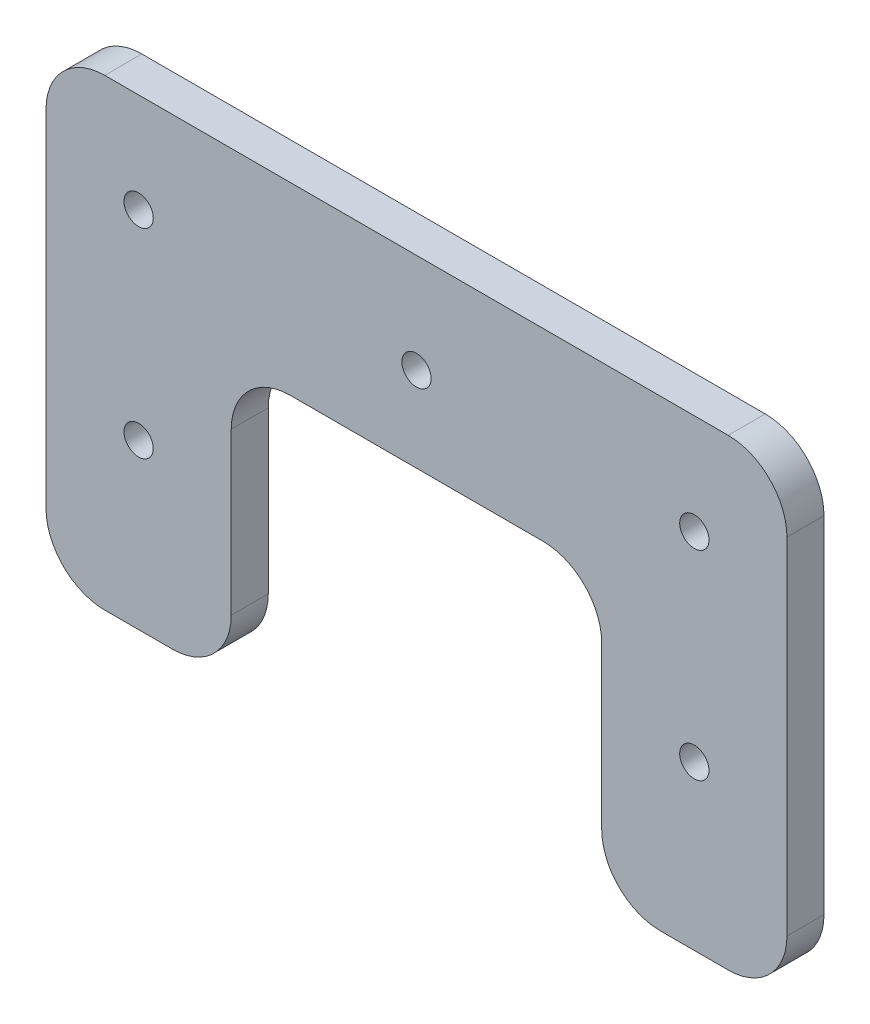
SolidWorks part; units mm, degrees
ref_plane "Alzado" through (0, 0, 0) normal (0, 0, 1) x (1, 0, 0)
ref_plane "Planta" through (0, 0, 0) normal (0, 1, 0) x (1, 0, 0)
ref_plane "Vista lateral" through (0, 0, 0) normal (1, 0, 0) x (0, 0, -1)
sketch "Croquis1" plane through (0, 0, 0) normal (0, 0, 1) x (1, 0, 0)
  line L1 (26.5381, 6.6994) -> (53.8381, 6.6994)
  line L2 (0.1881, 6.6044) -> (0.1881, 20.2544)
  line L3 (6.5381, 26.6044) -> (73.8381, 26.6044)
  line L4 (80.1881, 6.6044) -> (80.1881, 20.2544)
  line L6 (0.1881, 6.6044) -> (0.1881, -17.0456)
  line L7 (6.5381, -23.3956) -> (13.8381, -23.3956)
  line L8 (20.1881, 0.3494) -> (20.1881, -17.0456)
  line L10 (80.1881, 6.6044) -> (80.1881, -17.0456)
  line L11 (73.8381, -23.3956) -> (66.5381, -23.3956)
  line L12 (60.1881, 0.3494) -> (60.1881, -17.0456)
  circle A0 centre (40.1881, 15.8665) radius 1.58
  circle A1 centre (10.1881, 15.8665) radius 1.58
  circle A2 centre (70.1881, 15.7714) radius 1.58
  circle A3 centre (10.1881, -5.6765) radius 1.58
  circle A4 centre (70.1881, -5.7716) radius 1.58
  arc A5 (26.5381, 6.6994) -> (20.1881, 0.3494) centre (26.5381, 0.3494) ccw
  arc A6 (80.1881, 20.2544) -> (73.8381, 26.6044) centre (73.8381, 20.2544) ccw
  arc A7 (6.5381, 26.6044) -> (0.1881, 20.2544) centre (6.5381, 20.2544) ccw
  arc A8 (60.1881, 0.3494) -> (53.8381, 6.6994) centre (53.8381, 0.3494) ccw
  arc A9 (6.5381, -23.3956) -> (0.1881, -17.0456) centre (6.5381, -17.0456) cw
  arc A10 (13.8381, -23.3956) -> (20.1881, -17.0456) centre (13.8381, -17.0456) ccw
  arc A11 (73.8381, -23.3956) -> (80.1881, -17.0456) centre (73.8381, -17.0456) ccw
  arc A12 (66.5381, -23.3956) -> (60.1881, -17.0456) centre (66.5381, -17.0456) cw
  point P22 (20.1881, 6.6994)
  point P25 (80.1881, 26.6044)
  point P28 (0.1881, 26.6044)
  point P31 (60.1881, 6.6994)
  point P34 (0.1881, -23.3956)
  point P37 (20.1881, -23.3956)
  point P40 (80.1881, -23.3956)
  point P43 (60.1881, -23.3956)
  dimension "D7" = 3.16
  dimension "D8" = 3.16
  dimension "D9" = 3.16
  dimension "D10" = 3.16
  dimension "D11" = 3.16
  dimension "D14" = 10
  dimension "D19" = 6.35
  dimension "D20" = 6.35
  dimension "D21" = 6.35
  dimension "D1" = 20
  dimension "D2" = 80
  dimension "D3" = 30
  dimension "D4" = 20
  dimension "D5" = 30
  dimension "D6" = 20
  dimension "D12" = 20
  dimension "D13" = 40
  dimension "D15" = 10
  dimension "D16" = 10
  dimension "D17" = 10
  dimension "D18" = 40
extrude "Saliente-Extruir1" add sketch "Croquis1" along normal blind 4
